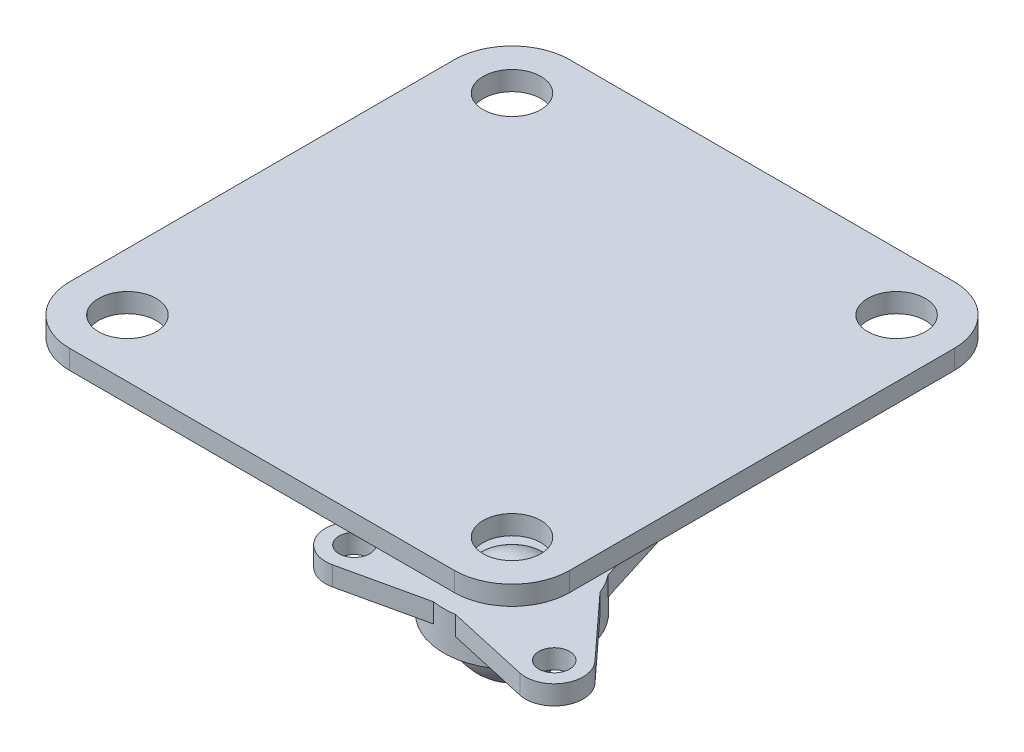
SolidWorks part; units mm, degrees
ref_plane "Front Plane" through (0, 0, 0) normal (0, 0, 1) x (1, 0, 0)
ref_plane "Top Plane" through (0, 0, 0) normal (0, 1, 0) x (1, 0, 0)
ref_plane "Right Plane" through (0, 0, 0) normal (1, 0, 0) x (0, 0, -1)
sketch "Sketch1" plane through (0, 0, 0) normal (0, 1, 0) x (1, 0, 0)
  line L1 (-10, -13) -> (10, -13)
  line L2 (-13, -10) -> (-13, 10)
  line L3 (-10, 13) -> (10, 13)
  line L4 (13, -10) -> (13, 10)
  line L5 (-13, -13) -> (13, 13) construction
  line L6 (-13, 13) -> (13, -13) construction
  circle A0 centre (-10, 10) radius 1.5
  circle A1 centre (10, 10) radius 1.5
  circle A2 centre (-10, -10) radius 1.5
  circle A3 centre (10, -10) radius 1.5
  arc A4 (-13, -10) -> (-10, -13) centre (-10, -10) ccw
  arc A5 (10, -13) -> (13, -10) centre (10, -10) ccw
  arc A6 (13, 10) -> (10, 13) centre (10, 10) ccw
  arc A7 (-13, 10) -> (-10, 13) centre (-10, 10) cw
  point P0 (0, 0)
  dimension "D3" = 3
  dimension "D5" = 3
  dimension "D1" = 26
  dimension "D2" = 26
  dimension "D4" = 20
extrude "Boss-Extrude1" add sketch "Sketch1" against normal blind 1
sketch "Sketch2" plane through (0, 0, 0) normal (0, 0, 1) x (1, 0, 0)
  line L0 (0, -13.45) -> (0, 0) construction
  line L1 (0, -10.9) -> (0, -16)
  arc A0 (0, -16) -> (0, -10.9) centre (0, -13.45) ccw
  point P2 (0, -16)
  dimension "D2" = 5.1
  dimension "D1" = 16
revolve "Revolve2" add sketch "Sketch2" angle 360 about L0
sketch "Sketch4" plane through (0, 0, 0) normal (0, 0, 1) x (1, 0, 0)
  line L0 (2.55, -13.45) -> (3.55, -13.45)
  line L1 (3.55, -13.45) -> (3.55, -11.45)
  line L2 (3.55, -11.45) -> (1.5819, -11.45)
  arc A0 (0, -16) -> (0, -10.9) centre (0, -13.45) ccw construction
  arc A1 (1.5819, -11.45) -> (2.55, -13.45) centre (0, -13.45) cw
  dimension "D1" = 1
  dimension "D2" = 2
revolve "Revolve3" add sketch "Sketch4" angle 360 about L0
sketch "Sketch5" plane through (0, -11.45, 0) normal (0, 1, 0) x (1, 0, 0)
  line L0 (-2.75, 2.245) -> (-1.4312, 6.449)
  line L2 (1.4312, 6.449) -> (2.75, 2.245)
  circle A0 centre (0, 0) radius 3.55 construction
  arc A1 (1.4312, 6.449) -> (-1.4312, 6.449) centre (0, 6) ccw
  circle A2 centre (0, 6) radius 0.8
  arc A3 (-2.75, 2.245) -> (2.75, 2.245) centre (0, 0) cw
  dimension "D1" = 1.5
  dimension "D4" = 1.6
  dimension "D2" = 6
  dimension "D3" = 5.5
extrude "Boss-Extrude2" add sketch "Sketch5" against normal blind 1
pattern_circular "CirPattern3" count 3 over 360 about axis through (0, 0, 0) along (0, 1, 0) of "Boss-Extrude2"
